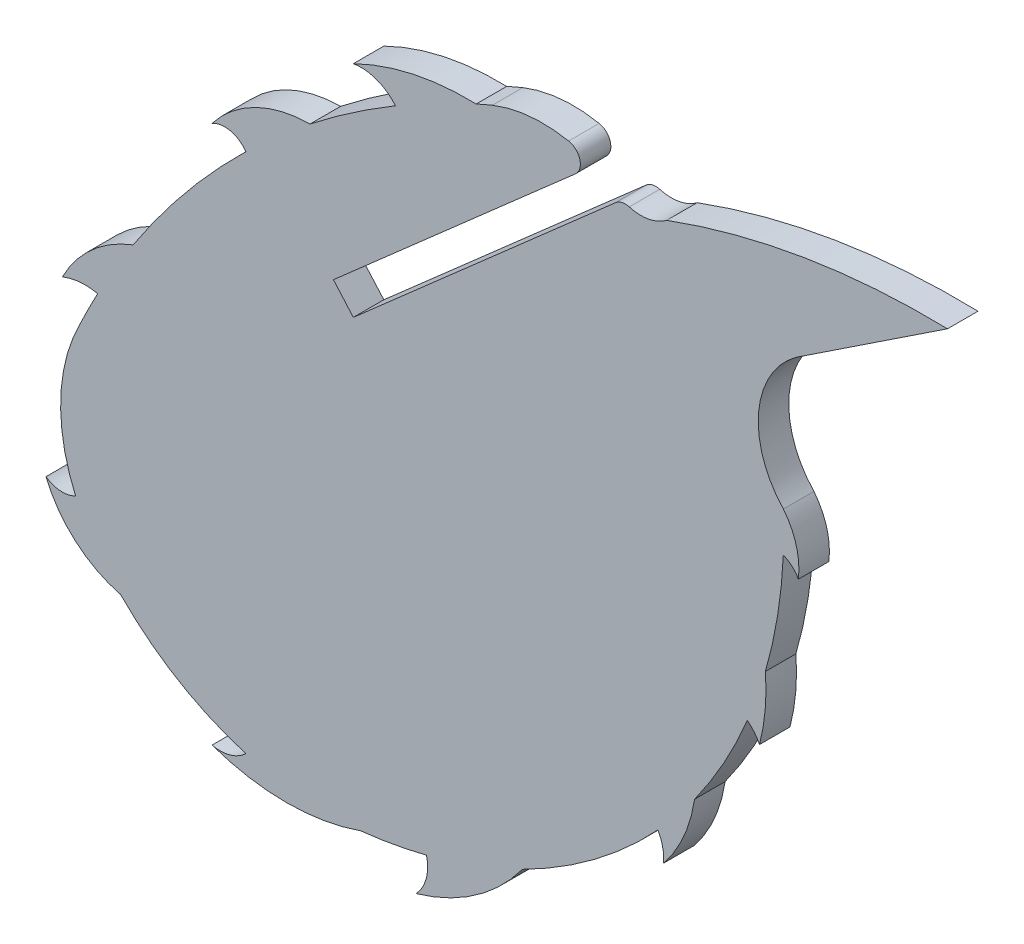
SolidWorks part; units mm, degrees
ref_plane "Front Plane" through (0, 0, 0) normal (0, 0, 1) x (1, 0, 0)
ref_plane "Top Plane" through (0, 0, 0) normal (0, 1, 0) x (1, 0, 0)
ref_plane "Right Plane" through (0, 0, 0) normal (1, 0, 0) x (0, 0, -1)
sketch "Sketch1" plane through (0, 0, 0) normal (0, 0, 1) x (1, 0, 0)
  line L0 (7.5687, 15.5826) -> (-5.5363, 4.0664)
  line L1 (-6.5303, 5.1983) -> (5.5562, 15.8191)
  line L2 (24.1403, 18.4092) -> (16.5607, 13.3842)
  line L3 (-5.5363, 4.0664) -> (-6.5303, 5.1983)
  arc A0 (-5.1722, -17.9617) -> (-1.8808, -17.3705) centre (-7.6992, 5.5658) ccw
  arc A1 (1.4095, 16.7154) -> (0.599, 16.3623) centre (16.9788, -20.1234) ccw
  arc A2 (5.2186, 17.0717) -> (1.4095, 16.7154) centre (3.9162, 10.457) ccw
  arc A3 (24.1403, 18.4092) -> (10.1151, 16.0907) centre (23.1688, -19.2941) ccw
  arc A4 (15.9445, 6.5183) -> (16.6903, 3.8536) centre (13.1793, 4.3077) cw
  arc A5 (16.6903, 3.8536) -> (15.9406, 4.5203) centre (15.4454, 3.2086) ccw
  arc A6 (16.5607, 13.3842) -> (15.9445, 6.5183) centre (19.2917, 9.6785) ccw
  arc A7 (8.2441, 15.7348) -> (10.1151, 16.0907) centre (8.8255, 17.7748) ccw
  arc A8 (8.2441, 15.7348) -> (7.5687, 15.5826) centre (8.046, 15.0394) ccw
  arc A9 (5.5562, 15.8191) -> (5.2186, 17.0717) centre (5.0789, 16.3623) ccw
  arc A10 (-17.1619, -13.7359) -> (-10.9026, -17.485) centre (-6.8426, -3.607) ccw
  arc A11 (-19.1701, -3.0132) -> (-19.4077, -10.5942) centre (-11.395, -7.0511) ccw
  arc A12 (15.0464, -0.9589) -> (14.7495, -4.2707) centre (5.0126, -1.7287) cw
  arc A13 (14.7495, -4.2707) -> (14.146, -3.5293) centre (12.9007, -5.1593) ccw
  arc A14 (15.0464, -0.9589) -> (15.9406, 4.5203) centre (-7.6992, 5.5658) ccw
  arc A15 (11.5072, -8.2561) -> (9.9606, -11.7945) centre (4.2797, -7.2041) cw
  arc A16 (9.9606, -11.7945) -> (9.6758, -10.4978) centre (7.7308, -11.6045) ccw
  arc A17 (11.5072, -8.2561) -> (14.146, -3.5293) centre (-7.6992, 5.5658) ccw
  arc A18 (2.9104, -15.5852) -> (-2.412, -19.2941) centre (-5.1722, -9.6596) cw
  arc A19 (-2.412, -19.2941) -> (-1.8808, -17.3705) centre (-3.8783, -17.854) ccw
  arc A20 (2.9104, -15.5852) -> (9.6758, -10.4978) centre (-7.6992, 5.5658) ccw
  arc A21 (-5.1722, -17.9617) -> (-12.5916, -17.9617) centre (-8.8819, -7.3713) cw
  arc A22 (-12.5916, -17.9617) -> (-10.9026, -17.485) centre (-12.1832, -16.1784) ccw
  arc A23 (-17.1619, -13.7359) -> (-20.886, -10.4978) centre (-15.8006, -8.4096) cw
  arc A24 (-20.886, -10.4978) -> (-19.4077, -10.5942) centre (-20.069, -9.3512) ccw
  arc A25 (0.599, 16.3623) -> (-5.5363, 15.0394) centre (0.1741, 3.4444) ccw
  arc A26 (-5.5363, 15.0394) -> (-3.4314, 14.2703) centre (-5.1498, 12.8323) cw
  arc A27 (-3.4314, 14.2703) -> (-7.6992, 11.3488) centre (16.9788, -20.1234) ccw
  arc A28 (-7.6992, 11.3488) -> (-12.5916, 8.933) centre (-7.6698, 5.1274) ccw
  arc A29 (-12.5916, 8.933) -> (-10.9026, 8.5494) centre (-11.9599, 7.8044) cw
  arc A30 (-10.9026, 8.5494) -> (-16.5343, 1.7025) centre (16.9788, -20.1234) ccw
  arc A31 (-16.5343, 1.7025) -> (-20.069, -1.4476) centre (-14.2227, -4.4495) ccw
  arc A32 (-20.069, -1.4476) -> (-18.3026, -1.2893) centre (-18.9246, -4.284) cw
  arc A33 (-18.3026, -1.2893) -> (-19.1701, -3.0132) centre (16.9788, -20.1234) ccw
extrude "Boss-Extrude1" add sketch "Sketch1" along normal blind 1.524
